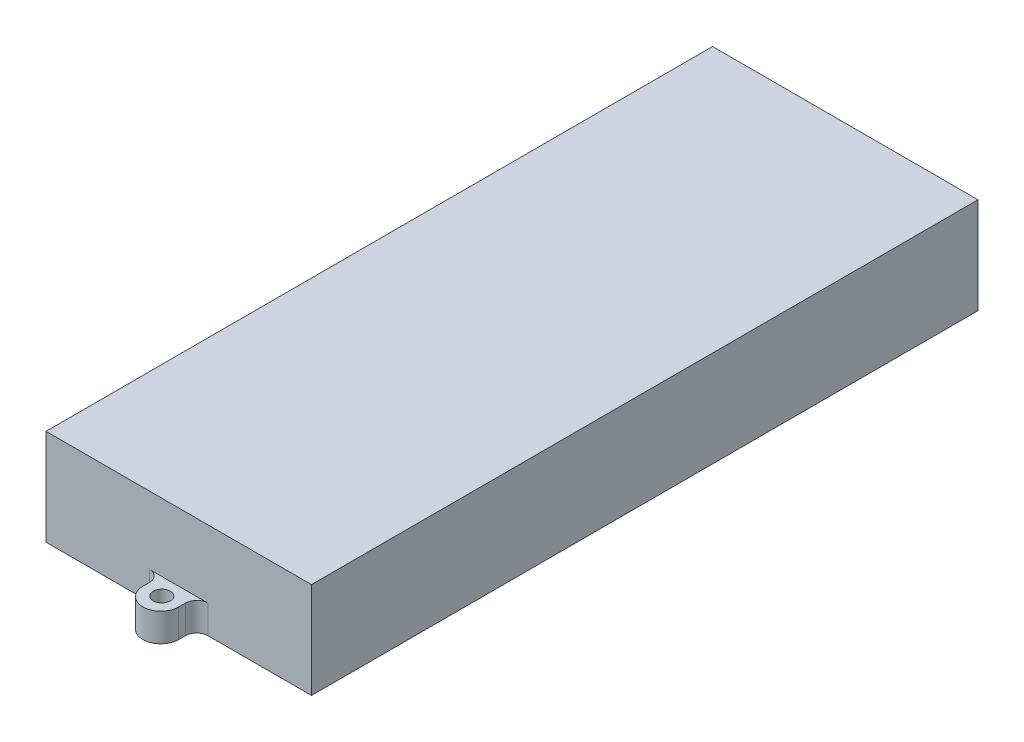
SolidWorks part; units mm, degrees
ref_plane "Front Plane" through (0, 0, 0) normal (0, 0, 1) x (1, 0, 0)
ref_plane "Top Plane" through (0, 0, 0) normal (0, 1, 0) x (1, 0, 0)
ref_plane "Right Plane" through (0, 0, 0) normal (1, 0, 0) x (0, 0, -1)
sketch "Sketch1" plane through (0, 0, 0) normal (0, 1, 0) x (1, 0, 0)
  line L1 (-23.5, -59) -> (23.5, -59)
  line L2 (-23.5, -59) -> (-23.5, 59)
  line L3 (-23.5, 59) -> (23.5, 59)
  line L4 (23.5, -59) -> (23.5, 59)
  line L5 (-23.5, -59) -> (23.5, 59) construction
  line L6 (-23.5, 59) -> (23.5, -59) construction
  point P0 (0, 0)
  dimension "D1" = 47
  dimension "D2" = 118
extrude "Boss-Extrude1" add sketch "Sketch1" along normal blind 17
sketch "Sketch2" plane through (0, 0, 0) normal (0, 1, 0) x (1, 0, 0)
  line L0 (-25.7921, 0) -> (26.5568, 0) construction
  line L1 (-3.175, 62.175) -> (-3.175, 59)
  line L6 (3.175, 62.175) -> (3.175, 59)
  line L7 (3.175, -62.175) -> (3.175, -59)
  line L9 (-3.175, -62.175) -> (-3.175, -59)
  line L10 (-3.175, 59) -> (3.175, 59)
  line L11 (-3.175, -59) -> (3.175, -59)
  arc A0 (3.175, 62.175) -> (-3.175, 62.175) centre (0, 62.175) ccw
  arc A1 (3.175, -62.175) -> (-3.175, -62.175) centre (0, -62.175) cw
  dimension "D1" = 6.35
  dimension "D2" = 59
extrude "Boss-Extrude2" add sketch "Sketch2" along normal blind 5
sketch "Sketch3" plane through (0, 5, 0) normal (0, 1, 0) x (1, 0, 0)
  line L0 (0, 0) -> (23.5, 0) construction
  line L1 (23.5, -59) -> (23.5, 59) construction
  line L2 (0, 65.35) -> (0, -65.35) construction
  circle A0 centre (0, -62) radius 1.5
  circle A1 centre (0, 62) radius 1.5
  arc A2 (3.175, 62.175) -> (-3.175, 62.175) centre (0, 62.175) ccw construction
  arc A3 (-3.175, -62.175) -> (3.175, -62.175) centre (0, -62.175) ccw construction
  dimension "D1" = 3
  dimension "D2" = 124
extrude "Cut-Extrude1" cut sketch "Sketch3" against normal through all
fillet "Fillet2" radius 2 4 edges at (3.175, 2.5, -59) (-3.175, 2.5, -59) (-3.175, 2.5, 59) (3.175, 2.5, 59)
